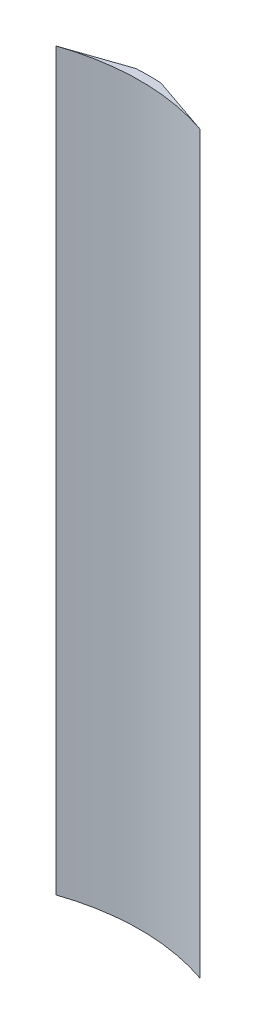
SolidWorks part; units mm, degrees
material "6061-T6 (SS)"
ref_plane "Front Plane" through (0, 0, 0) normal (0, 0, 1) x (1, 0, 0)
ref_plane "Top Plane" through (0, 0, 0) normal (0, 1, 0) x (1, 0, 0)
ref_plane "Right Plane" through (0, 0, 0) normal (1, 0, 0) x (0, 0, -1)
sketch "Sketch2" plane through (0, 0, 0) normal (0, 1, 0) x (1, 0, 0)
  line L0 (0, 0) -> (0, 56.4183) construction
  line L1 (-2.2557, 41.6585) -> (-13.0366, 37.9556)
  line L2 (2.2578, 41.6584) -> (13.0385, 37.9549)
  arc A0 (13.0385, 37.9549) -> (-13.0366, 37.9556) centre (0, 0) ccw
  arc A2 (2.2578, 41.6584) -> (-2.2557, 41.6585) centre (0, 0) ccw
  dimension "D2" = 80.264
  dimension "D3" = 2.2557
  dimension "D4" = 2.2578
extrude "Boss-Extrude1" add sketch "Sketch2" along normal blind 133.35
